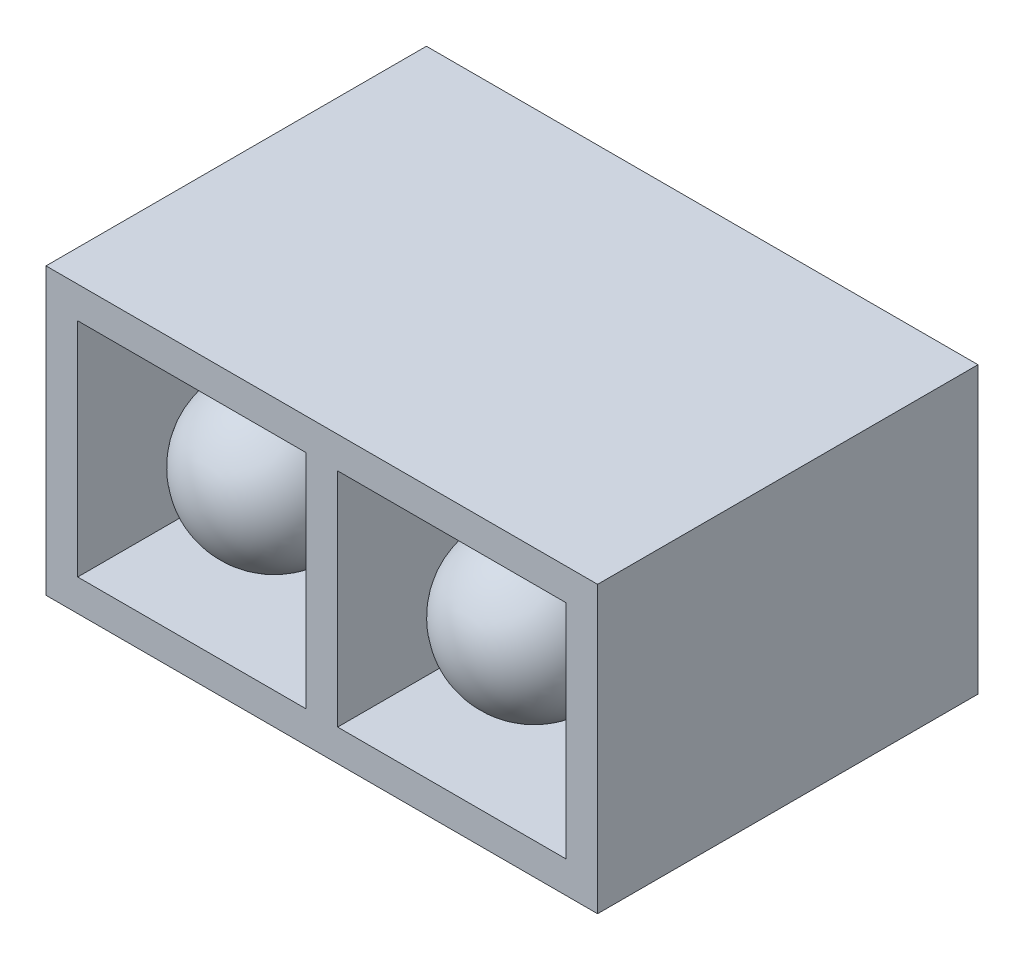
SolidWorks part; units mm, degrees
ref_plane "Plan de face" through (0, 0, 0) normal (0, 0, 1) x (1, 0, 0)
ref_plane "Plan de dessus" through (0, 0, 0) normal (0, 1, 0) x (1, 0, 0)
ref_plane "Plan de droite" through (0, 0, 0) normal (1, 0, 0) x (0, 0, -1)
sketch "Esquisse1" plane through (0, 0, 0) normal (0, 0, 1) x (1, 0, 0)
  line L0 (0, 2.87) -> (0, -2.5096) construction
  line L1 (-4.9678, 0) -> (4.8391, 0) construction
  line L3 (-4.35, 2.25) -> (4.35, 2.25)
  line L4 (-4.35, 2.25) -> (-4.35, -2.25)
  line L5 (-4.35, -2.25) -> (4.35, -2.25)
  line L6 (4.35, 2.25) -> (4.35, -2.25)
  dimension "D1" = 8.7
  dimension "D2" = 4.5
extrude "Extru.-Mince1" add sketch "Esquisse1" along normal blind 6 thin
sketch "Esquisse2" plane through (0, 0, 0) normal (0, 0, 1) x (1, 0, 0)
  line L0 (0, 2.5012) -> (0, -2.5302) construction
  line L2 (4.35, 2.25) -> (-4.35, 2.25) construction
  line L3 (-0.25, 2.25) -> (0.25, 2.25)
  line L4 (-0.25, 2.25) -> (-0.25, -2.25)
  line L5 (-0.25, -2.25) -> (0.25, -2.25)
  line L6 (0.25, 2.25) -> (0.25, -2.25)
  line L7 (-4.35, -2.25) -> (4.35, -2.25) construction
  dimension "D2" = 0.5
extrude "Boss.-Extru.1" add sketch "Esquisse2" along normal blind 6
sketch "Esquisse3" plane through (0, 0, 0) normal (0, 0, -1) x (-1, 0, 0)
  line L1 (-4.35, 2.25) -> (4.35, 2.25)
  line L2 (-4.35, 2.25) -> (-4.35, -2.25)
  line L3 (-4.35, -2.25) -> (4.35, -2.25)
  line L4 (4.35, 2.25) -> (4.35, -2.25)
extrude "Boss.-Extru.2" add sketch "Esquisse3" against normal blind 2
sketch "Esquisse5" plane through (0, 0, 0) normal (0, 1, 0) x (1, 0, 0)
  line L0 (-2.05, -1.1845) -> (-2.05, -6.5255) construction
  line L2 (-0.3863, -4.7) -> (-3.2833, -4.7) construction
  line L4 (-3.25, -4.7) -> (-3.25, -2)
  line L5 (-3.25, -2) -> (-2.05, -2)
  line L7 (4.35, -6) -> (-4.35, -6) construction
  line L8 (-2.05, -2) -> (-2.05, -5.9)
  line L9 (4.35, 0) -> (-4.35, 0) construction
  line L11 (-0.25, -2) -> (-0.25, -6) construction
  line L12 (-3.85, -6) -> (-3.85, -2) construction
  arc A0 (-3.25, -4.7) -> (-2.05, -5.9) centre (-2.05, -4.7) ccw
  point P4 (-3.2833, -4.8751)
  point P18 (0, 0)
  dimension "D1" = 2
  dimension "D2" = 1.2
  dimension "D3" = 0.1
revolve "Révolution1" add sketch "Esquisse5" angle 360 about L0
sketch "Esquisse6" plane through (0, 0, 0) normal (0, 1, 0) x (1, 0, 0)
  line L0 (2.05, -1.4061) -> (2.05, -6.3604) construction
  line L1 (0.25, -6) -> (0.25, -2) construction
  line L2 (3.85, -6) -> (3.85, -2) construction
  line L3 (2.05, -4.7) -> (0.469, -4.7) construction
  line L4 (4.35, -6) -> (-4.35, -6) construction
  line L5 (0.85, -4.7) -> (0.85, -2)
  line L6 (0.25, -2) -> (3.85, -2) construction
  line L7 (0.85, -2) -> (2.05, -2)
  line L8 (2.05, -2) -> (2.05, -5.9)
  arc A0 (0.85, -4.7) -> (2.05, -5.9) centre (2.05, -4.7) ccw
  dimension "D1" = 2.4
  dimension "D2" = 0.1
revolve "Révolution2" add sketch "Esquisse6" angle 360 about L0
